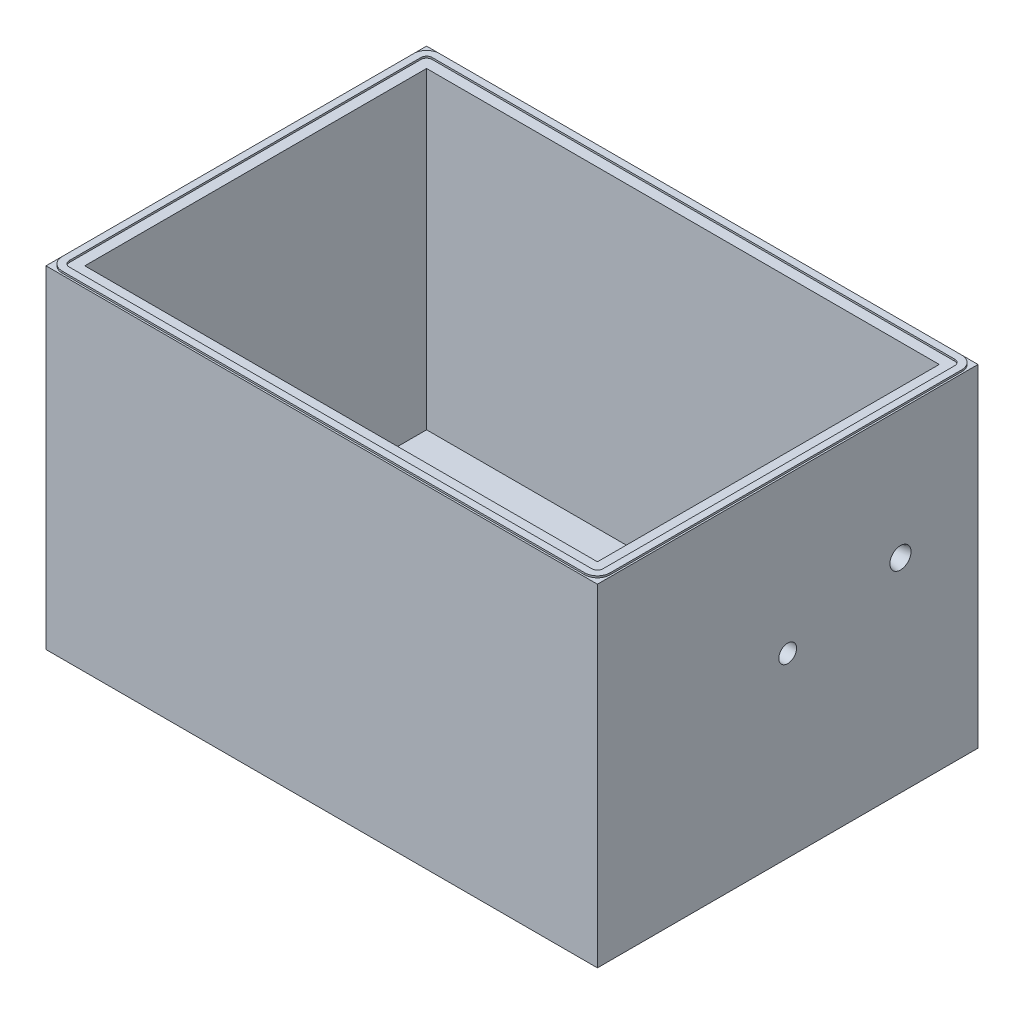
SolidWorks part; units mm, degrees
material "Acrylic (Medium-high impact)"
ref_plane "Front Plane" through (0, 0, 0) normal (0, 0, 1) x (1, 0, 0)
ref_plane "Top Plane" through (0, 0, 0) normal (0, 1, 0) x (1, 0, 0)
ref_plane "Right Plane" through (0, 0, 0) normal (1, 0, 0) x (0, 0, -1)
sketch "Sketch1" plane through (0, 0, 0) normal (0, 1, 0) x (1, 0, 0)
  line L1 (-248.412, -171.45) -> (248.412, -171.45)
  line L2 (-248.412, -171.45) -> (-248.412, 171.45)
  line L3 (-248.412, 171.45) -> (248.412, 171.45)
  line L4 (248.412, -171.45) -> (248.412, 171.45)
  line L5 (-248.412, -171.45) -> (248.412, 171.45) construction
  line L6 (-248.412, 171.45) -> (248.412, -171.45) construction
  point P0 (0, 0)
  dimension "D1" = 342.9
  dimension "D2" = 496.824
extrude "Boss-Extrude1" add sketch "Sketch1" along normal blind 17.4625
sketch "Sketch2" plane through (0, 17.4625, 0) normal (0, 1, 0) x (1, 0, 0)
  line L4 (-248.412, 171.45) -> (-248.412, -171.45) construction
  line L5 (-248.412, 171.45) -> (-248.412, -171.45)
  line L6 (-248.412, -171.45) -> (248.412, -171.45) construction
  line L7 (248.412, -171.45) -> (248.412, 171.45) construction
  line L8 (230.9495, -153.9875) -> (230.9495, 153.9875)
  line L9 (230.9495, 153.9875) -> (-230.9495, 153.9875)
  line L10 (-230.9495, 153.9875) -> (-230.9495, -153.9875)
  line L11 (-230.9495, -153.9875) -> (230.9495, -153.9875)
  line L12 (230.9495, -153.9875) -> (230.9495, 153.9875)
  line L13 (230.9495, 153.9875) -> (-230.9495, 153.9875)
  line L14 (-230.9495, 153.9875) -> (-230.9495, -153.9875)
  line L15 (-230.9495, -153.9875) -> (230.9495, -153.9875)
  line L16 (248.412, 171.45) -> (-248.412, 171.45) construction
  line L17 (-248.412, -171.45) -> (248.412, -171.45)
  line L18 (248.412, -171.45) -> (248.412, 171.45)
  line L19 (248.412, 171.45) -> (-248.412, 171.45)
  dimension "D1" = 17.4625
extrude "Boss-Extrude2" add sketch "Sketch2" along direction (0, -1, 0) on the side of the normal blind 301 from surface at -17.4625 starting at face at (0, 0, 0)
sketch "Sketch11" plane through (0, 301, 0) normal (0, 1, 0) x (1, 0, 0)
  line L8 (-230.9495, -153.9875) -> (230.9495, -153.9875) construction
  line L9 (230.9495, -153.9875) -> (230.9495, 153.9875) construction
  line L10 (-230.9495, 153.9875) -> (-230.9495, -153.9875) construction
  line L11 (230.9495, 153.9875) -> (-230.9495, 153.9875) construction
  line L12 (-230.9495, -153.9875) -> (230.9495, -153.9875)
  line L13 (230.9495, -153.9875) -> (230.9495, 153.9875)
  line L14 (-230.9495, 153.9875) -> (-230.9495, -153.9875)
  line L15 (230.9495, 153.9875) -> (-230.9495, 153.9875)
  line L16 (235.3945, 163.5125) -> (-235.3945, 163.5125)
  line L17 (-240.4745, 158.4325) -> (-240.4745, -158.4325)
  line L18 (-235.3945, -163.5125) -> (235.3945, -163.5125)
  line L19 (240.4745, -158.4325) -> (240.4745, 158.4325)
  line L20 (240.4745, 163.5125) -> (-240.4745, 163.5125) construction
  line L21 (240.4745, -163.5125) -> (240.4745, 163.5125) construction
  line L22 (-240.4745, -163.5125) -> (240.4745, -163.5125) construction
  line L23 (-240.4745, 163.5125) -> (-240.4745, -163.5125) construction
  arc A0 (235.3945, 163.5125) -> (240.4745, 158.4325) centre (235.3945, 158.4325) cw
  arc A1 (235.3945, -163.5125) -> (240.4745, -158.4325) centre (235.3945, -158.4325) ccw
  arc A2 (-240.4745, -158.4325) -> (-235.3945, -163.5125) centre (-235.3945, -158.4325) ccw
  arc A3 (-235.3945, 163.5125) -> (-240.4745, 158.4325) centre (-235.3945, 158.4325) ccw
  dimension "D2" = 5.08
  dimension "D1" = 9.525
extrude "Cut-Extrude2" cut sketch "Sketch11" against normal blind 1.5875
sketch "Sketch30" plane through (248.412, 0, 0) normal (1, 0, 0) x (0, 0, -1)
  line L0 (101.6, 301) -> (101.6, 183.525) construction
  line L2 (101.6, 183.525) -> (171.45, 183.525) construction
  line L3 (171.45, 301) -> (171.45, 0) construction
  line L4 (171.45, 301) -> (-171.45, 301) construction
  circle A0 centre (101.6, 183.525) radius 9.525
  dimension "D3" = 19.05
  dimension "D1" = 117.475
  dimension "D2" = 69.85
extrude "Cut-Extrude4" cut sketch "Sketch30" against normal up to next (17.4625 mm away) draft 10.304
sketch "Sketch34" plane through (0, 301, 0) normal (0, 1, 0) x (1, 0, 0)
  line L0 (-248.412, -171.45) -> (-248.412, 171.45) construction
  line L1 (248.412, -171.45) -> (-248.412, -171.45) construction
  line L2 (-248.412, 171.45) -> (248.412, 171.45) construction
  line L3 (248.412, 171.45) -> (248.412, -171.45) construction
  line L4 (-248.412, -171.45) -> (-248.412, 171.45)
  line L5 (248.412, -171.45) -> (-248.412, -171.45)
  line L6 (-248.412, 171.45) -> (248.412, 171.45)
  line L7 (248.412, 171.45) -> (248.412, -171.45)
  line L22 (-235.3945, -169.8625) -> (235.3945, -169.8625)
  line L23 (-246.8245, 158.4325) -> (-246.8245, -158.4325)
  line L24 (235.3945, 169.8625) -> (-235.3945, 169.8625)
  line L25 (246.8245, -158.4325) -> (246.8245, 158.4325)
  line L26 (-235.3945, -169.8625) -> (235.3945, -169.8625)
  line L27 (-246.8245, 158.4325) -> (-246.8245, -158.4325)
  line L28 (235.3945, 169.8625) -> (-235.3945, 169.8625)
  line L29 (246.8245, -158.4325) -> (246.8245, 158.4325)
  arc A12 (235.3945, -169.8625) -> (246.8245, -158.4325) centre (235.3945, -158.4325) ccw
  arc A13 (-246.8245, -158.4325) -> (-235.3945, -169.8625) centre (-235.3945, -158.4325) ccw
  arc A14 (-235.3945, 169.8625) -> (-246.8245, 158.4325) centre (-235.3945, 158.4325) ccw
  arc A15 (246.8245, 158.4325) -> (235.3945, 169.8625) centre (235.3945, 158.4325) ccw
  arc A16 (235.3945, -169.8625) -> (246.8245, -158.4325) centre (235.3945, -158.4325) ccw
  arc A17 (-246.8245, -158.4325) -> (-235.3945, -169.8625) centre (-235.3945, -158.4325) ccw
  arc A18 (-235.3945, 169.8625) -> (-246.8245, 158.4325) centre (-235.3945, 158.4325) ccw
  arc A19 (246.8245, 158.4325) -> (235.3945, 169.8625) centre (235.3945, 158.4325) ccw
  dimension "D1" = 6.35
extrude "Cut-Extrude5" cut sketch "Sketch34" against normal blind 1.5875
sketch "Sketch35" plane through (248.412, 0, 0) normal (1, 0, 0) x (0, 0, -1)
  line L0 (0, 159.7125) -> (0, 0) construction
  line L1 (-171.45, 0) -> (171.45, 0) construction
  circle A0 centre (0, 159.7125) radius 8.001
  dimension "D1" = 16.002
extrude "Cut-Extrude6" cut sketch "Sketch35" against normal up to next
equation "\".75n\"=1"
